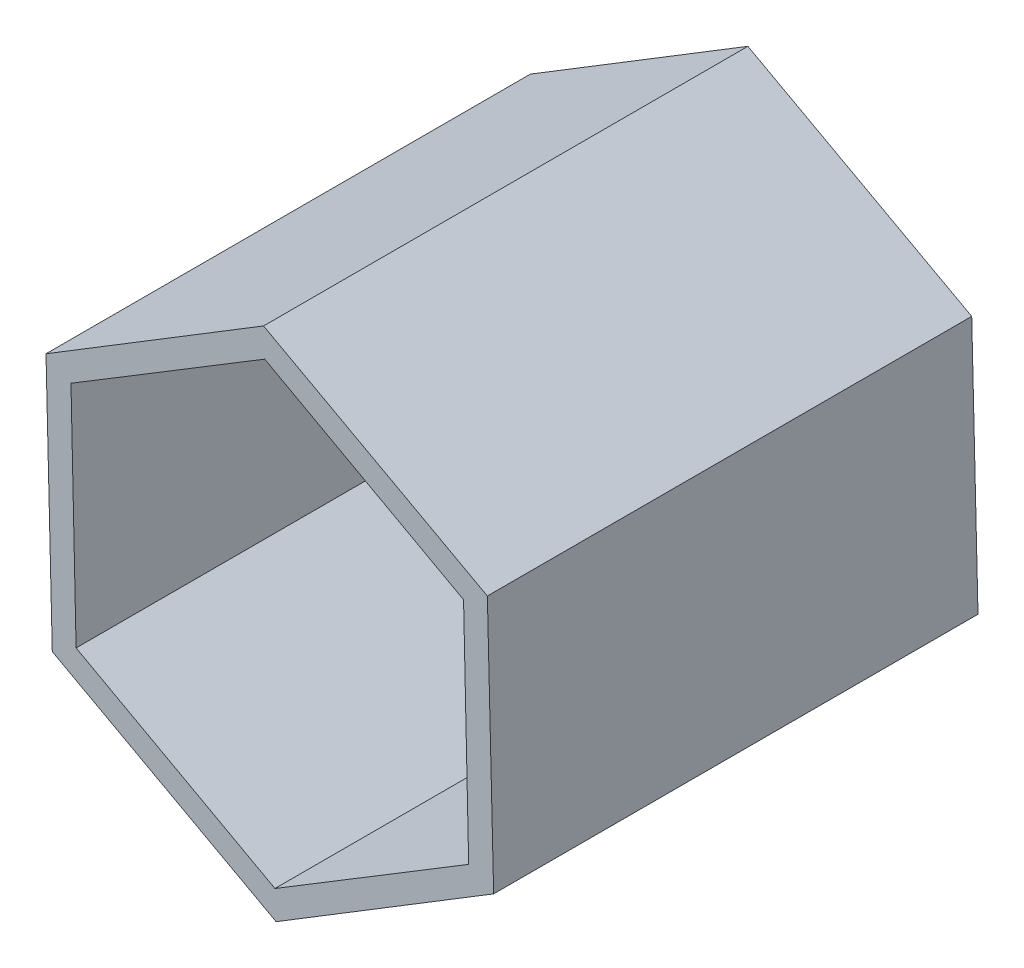
SolidWorks part; units mm, degrees
ref_plane "Front Plane" through (0, 0, 0) normal (0, 0, 1) x (1, 0, 0)
ref_plane "Top Plane" through (0, 0, 0) normal (0, 1, 0) x (1, 0, 0)
ref_plane "Right Plane" through (0, 0, 0) normal (1, 0, 0) x (0, 0, -1)
sketch "Sketch1" plane through (0, 0, 0) normal (0, 0, 1) x (1, 0, 0)
  line L1 (57.0414, 34.8366) -> (-1.6487, 66.8176)
  line L2 (-1.6487, 66.8176) -> (-58.6901, 31.981)
  line L3 (-58.6901, 31.981) -> (-57.0414, -34.8366)
  line L4 (-57.0414, -34.8366) -> (1.6487, -66.8176)
  line L5 (1.6487, -66.8176) -> (58.6901, -31.981)
  line L6 (58.6901, -31.981) -> (57.0414, 34.8366)
  circle A0 centre (0, 0) radius 57.8834 construction
extrude "Boss-Extrude1" add sketch "Sketch1" along normal blind 127
sketch "Sketch2" plane through (0, 0, 127) normal (0, 0, 1) x (1, 0, 0)
  line L1 (50.7991, 30.8794) -> (-1.3428, 59.433)
  line L2 (-1.3428, 59.433) -> (-52.1419, 28.5536)
  line L3 (-52.1419, 28.5536) -> (-50.7991, -30.8794)
  line L4 (-50.7991, -30.8794) -> (1.3428, -59.433)
  line L5 (1.3428, -59.433) -> (52.1419, -28.5536)
  line L6 (52.1419, -28.5536) -> (50.7991, 30.8794)
  circle A0 centre (0, 0) radius 51.4836 construction
extrude "Cut-Extrude1" cut sketch "Sketch2" against normal blind 127
